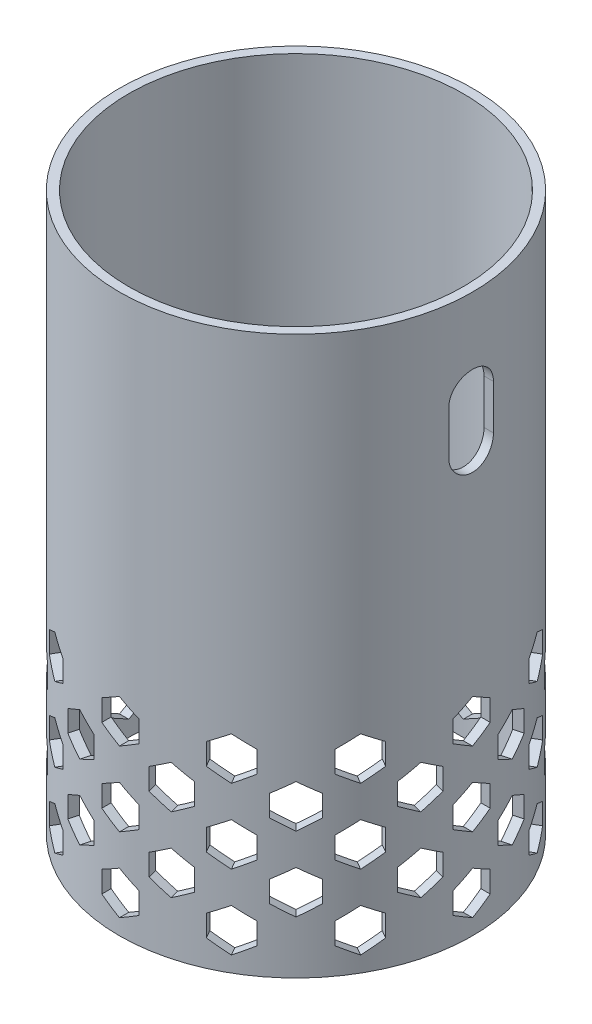
SolidWorks part; units mm, degrees
ref_plane "Front Plane" through (0, 0, 0) normal (0, 0, 1) x (1, 0, 0)
ref_plane "Top Plane" through (0, 0, 0) normal (0, 1, 0) x (1, 0, 0)
ref_plane "Right Plane" through (0, 0, 0) normal (1, 0, 0) x (0, 0, -1)
sketch "Sketch1" plane through (0, 0, 0) normal (0, 1, 0) x (1, 0, 0)
  circle A0 centre (0, 0) radius 45
  circle A1 centre (0, 0) radius 47.5
  dimension "D1" = 90
  dimension "D2" = 2.5
extrude "Boss-Extrude1" add sketch "Sketch1" along normal blind 150
sketch "Sketch2" plane through (0, 0, 0) normal (1, 0, 0) x (0, 0, -1)
  line L0 (0, 126) -> (0, 114) construction
  line L1 (6, 126) -> (6, 114)
  line L2 (-6, 126) -> (-6, 114)
  line L3 (47.5, 150) -> (-47.5, 150) construction
  arc A0 (6, 126) -> (-6, 126) centre (0, 126) ccw
  arc A1 (-6, 114) -> (6, 114) centre (0, 114) ccw
  point P3 (0, 120)
  dimension "D3" = 6
  dimension "D1" = 30
  dimension "D2" = 12
extrude "Cut-Extrude1" cut sketch "Sketch2" along normal blind 150
sketch "Sketch3" plane through (0, 0, 0) normal (1, 0, 0) x (0, 0, -1)
  line L0 (0, 0) -> (0, 10) construction
  line L2 (0, 4.2265) -> (5, 7.1132)
  line L3 (5, 7.1132) -> (5, 12.8868)
  line L4 (5, 12.8868) -> (0, 15.7735)
  line L5 (0, 15.7735) -> (-5, 12.8868)
  line L6 (-5, 12.8868) -> (-5, 7.1132)
  line L7 (-5, 7.1132) -> (0, 4.2265)
  circle A0 centre (0, 10) radius 5 construction
  dimension "D2" = 10
  dimension "D1" = 10
extrude "Cut-Extrude2" cut sketch "Sketch3" against normal through all both and the other way through all
pattern_circular "CirPattern1" count 12 over 360 about axis through (0, 0, 0) along (0, 1, 0) of "Cut-Extrude2"
sketch "Sketch4" plane through (0, 0, 0) normal (1, 0, 0) x (0, 0, -1)
  line L0 (0, -28.5017) -> (0, 166.736) construction
ref_plane "Plane1" through (0, 0, 0) normal (-0.9659, 0, 0.2588) x (0, 1, 0)
sketch "Sketch5" plane through (0, 0, 0) normal (-0.9659, 0, 0.2588) x (0, 1, 0)
  line L0 (0, 0) -> (20, 0) construction
  line L1 (-28.5017, 0) -> (166.736, 0) construction
  line L3 (14.2265, 0) -> (17.1132, -5)
  line L4 (17.1132, -5) -> (22.8868, -5)
  line L5 (22.8868, -5) -> (25.7735, 0)
  line L6 (25.7735, 0) -> (22.8868, 5)
  line L7 (22.8868, 5) -> (17.1132, 5)
  line L8 (17.1132, 5) -> (14.2265, 0)
  circle A0 centre (20, 0) radius 5 construction
  dimension "D2" = 10
  dimension "D1" = 20
extrude "Cut-Extrude3" cut sketch "Sketch5" against normal through all both 130
pattern_circular "CirPattern2" count 12 over 360 about axis through (0, 0, 0) along (0, 1, 0) of "Cut-Extrude3"
pattern_linear "LPattern2" count 2 spacing 20 along (0, 1, 0) of "CirPattern2", "Cut-Extrude3"
pattern_linear "LPattern3" count 3 spacing 20 along (0, 1, 0) of "CirPattern1", "Cut-Extrude2"
